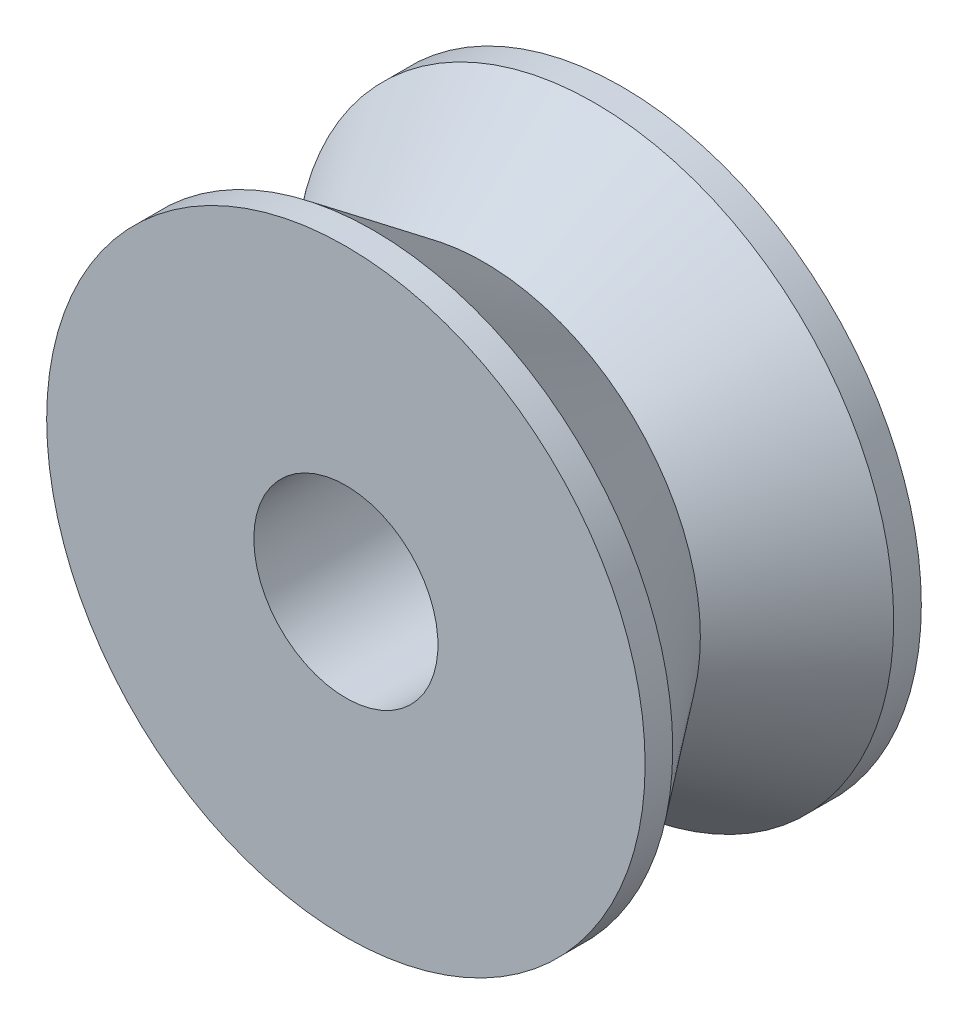
SolidWorks part; units mm, degrees
ref_plane "前视基准面" through (0, 0, 0) normal (0, 0, 1) x (1, 0, 0)
ref_plane "上视基准面" through (0, 0, 0) normal (0, 1, 0) x (1, 0, 0)
ref_plane "右视基准面" through (0, 0, 0) normal (1, 0, 0) x (0, 0, -1)
sketch "草图1" plane through (0, 0, 0) normal (1, 0, 0) x (0, 0, -1)
  line L0 (0, 0) -> (0, 25.85) construction
  line L1 (-3, 2) -> (3, 2)
  line L2 (3, 2) -> (3, 6.5)
  line L3 (3, 6.5) -> (2.4, 6.5)
  line L4 (2.4, 6.5) -> (0, 4.7)
  line L5 (-2.4, 6.5) -> (0, 4.7)
  line L6 (-3, 6.5) -> (-2.4, 6.5)
  line L7 (-3, 2) -> (-3, 6.5)
  line L8 (0, 0) -> (-4.6037, 0) construction
  point P12 (0, 2)
  dimension "D1" = 2.4
  dimension "D2" = 6.5
  dimension "D3" = 3
  dimension "D4" = 1.8
  dimension "D5" = 2
revolve "旋转1" add sketch "草图1" angle 360 about L8
